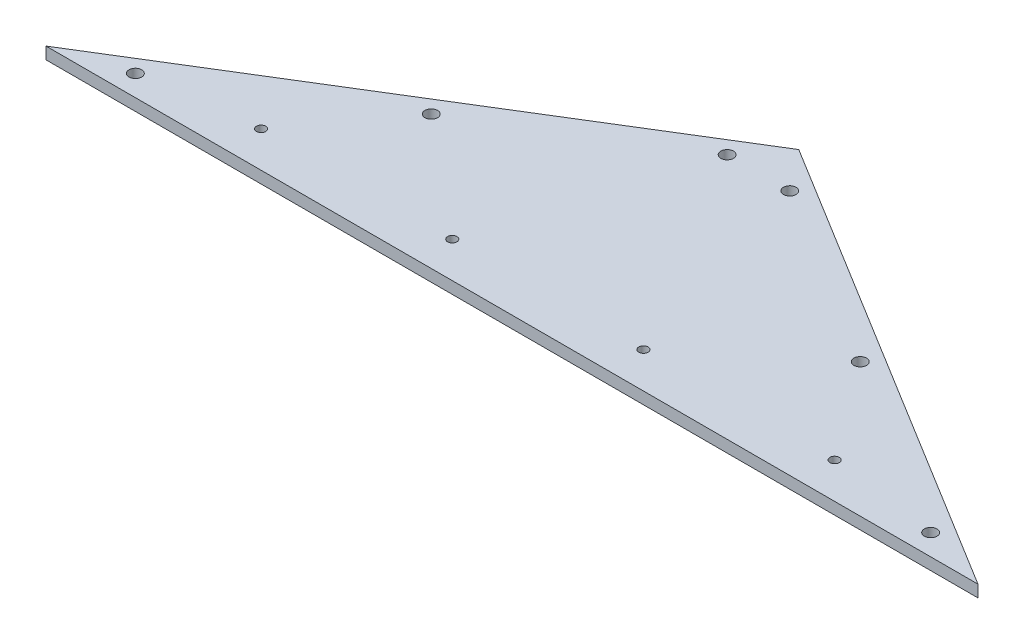
SolidWorks part; units mm, degrees
material "PC High Viscosity"
ref_plane "Front Plane" through (0, 0, 0) normal (0, 0, 1) x (1, 0, 0)
ref_plane "Top Plane" through (0, 0, 0) normal (0, 1, 0) x (1, 0, 0)
ref_plane "Right Plane" through (0, 0, 0) normal (1, 0, 0) x (0, 0, -1)
sketch "Sketch1" plane through (0, 0, 0) normal (0, 1, 0) x (1, 0, 0)
  line L1 (0, 0) -> (247.65, 152.4)
  line L2 (247.65, 152.4) -> (495.3, 0)
  line L4 (495.3, 0) -> (0, 0)
  dimension "D1" = 152.4
  dimension "D3" = 495.3
extrude "Boss-Extrude1" add sketch "Sketch1" along normal blind 6.35
sketch "Sketch2" plane through (0, 6.35, 0) normal (0, 1, 0) x (1, 0, 0)
  line L0 (0, 0) -> (495.3, 0) construction
  circle A0 centre (95.25, 19.05) radius 2.4638
  point P4 (247.65, 0)
  dimension "D1" = 152.4
  dimension "D3" = 4.9276
  dimension "D2" = 19.05
extrude "Cut-Extrude1" cut sketch "Sketch2" against normal through all
pattern_linear "LPattern1" count 4 spacing 101.6 along (1, 0, 0) of "Cut-Extrude1"
sketch "Sketch3" plane through (0, 6.35, 0) normal (0, 1, 0) x (1, 0, 0)
  line L0 (247.65, 141.2159) -> (18.1741, 0) construction
  line L1 (247.65, 141.2159) -> (477.1259, 0) construction
  line L2 (247.65, 152.4) -> (0, 0) construction
  line L3 (495.3, 0) -> (247.65, 152.4) construction
  line L4 (0, 0) -> (495.3, 0) construction
  line L5 (247.65, 152.4) -> (215.78, 204.1887) construction
  circle A0 centre (231.0099, 130.9759) radius 3.3655
  circle A1 centre (133.6654, 71.0715) radius 3.3655
  circle A2 centre (36.3208, 11.1672) radius 3.3655
  circle A3 centre (264.2901, 130.9759) radius 3.3655
  circle A4 centre (361.6346, 71.0715) radius 3.3655
  circle A5 centre (458.9792, 11.1672) radius 3.3655
  dimension "D3" = 25.4
  dimension "D6" = 6.731
  dimension "D1" = 9.525
  dimension "D2" = 9.525
  dimension "D4" = 139.7
  dimension "D5" = 254
extrude "Cut-Extrude2" cut sketch "Sketch3" against normal through all
